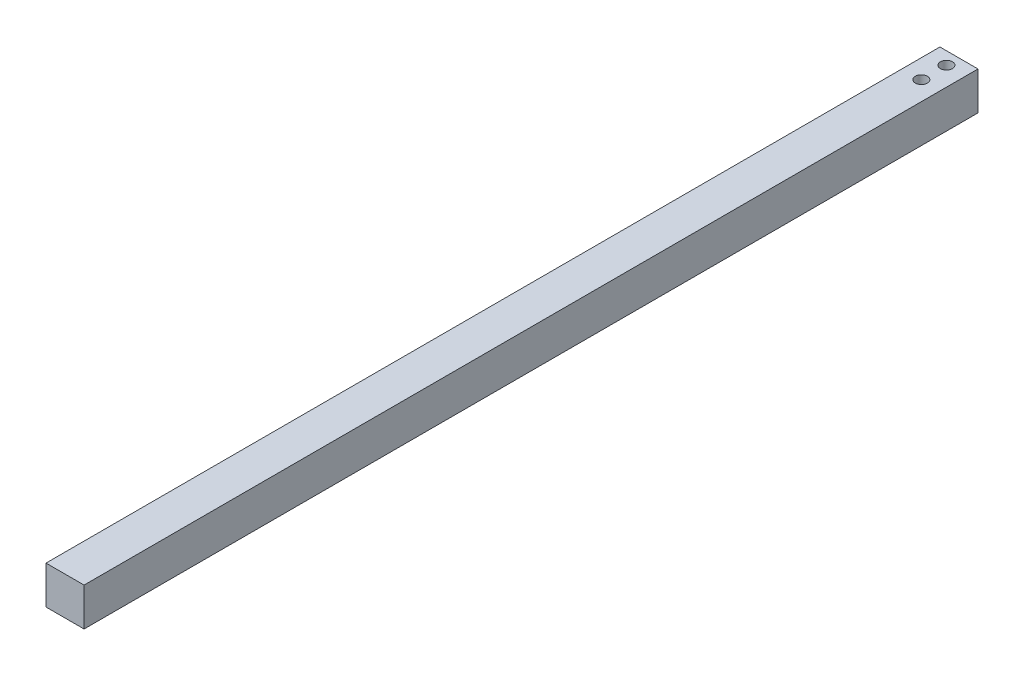
SolidWorks part; units mm, degrees
ref_plane "Front Plane" through (0, 0, 0) normal (0, 0, 1) x (1, 0, 0)
ref_plane "Top Plane" through (0, 0, 0) normal (0, 1, 0) x (1, 0, 0)
ref_plane "Right Plane" through (0, 0, 0) normal (1, 0, 0) x (0, 0, -1)
sketch "Sketch1" plane through (0, 0, 0) normal (0, 0, 1) x (1, 0, 0)
  line L1 (-9.5, -9.5) -> (9.5, -9.5)
  line L2 (-9.5, -9.5) -> (-9.5, 9.5)
  line L3 (-9.5, 9.5) -> (9.5, 9.5)
  line L4 (9.5, -9.5) -> (9.5, 9.5)
  line L5 (-9.5, -9.5) -> (9.5, 9.5) construction
  line L6 (-9.5, 9.5) -> (9.5, -9.5) construction
  point P0 (0, 0)
extrude "Boss-Extrude1" add sketch "Sketch1" along normal blind 446
sketch "Sketch2" plane through (0, -9.5, 0) normal (0, -1, 0) x (1, 0, 0)
  line L0 (-9.5, 446) -> (9.5, 446) construction
  line L1 (-9, 438.5) -> (9, 438.5)
  line L2 (-9, 438.5) -> (-9, 453.5)
  line L3 (-9, 453.5) -> (9, 453.5)
  line L4 (9, 438.5) -> (9, 453.5)
  line L5 (-9, 438.5) -> (9, 453.5) construction
  line L6 (-9, 453.5) -> (9, 438.5) construction
  line L7 (9, 446) -> (9, 438.5)
  line L8 (9, 438.5) -> (9, 442.25)
  line L9 (9, 442.25) -> (-9, 442.25)
  line L10 (9, 442.25) -> (6, 442.25)
  line L11 (0, 446) -> (0, 438.5)
  circle A0 centre (6, 442.25) radius 2
  circle A1 centre (-6, 442.25) radius 2
  point P0 (0, 446)
extrude "Cut-Extrude1" cut sketch "Sketch2" against normal blind 9 contours A1 L9 | A1 L9 | L10 A0 L9 | L9 A0 L10
sketch "Sketch3" plane through (0, 9.5, 0) normal (0, 1, 0) x (1, 0, 0)
  line L0 (9.5, 0) -> (-9.5, 0) construction
  line L1 (9.5, 0) -> (-9.5, 0)
  line L2 (0, 0) -> (0, -25)
  line L3 (0, -25) -> (0, -12.5)
  line L4 (0, -12.5) -> (-6.1481, -12.5)
  circle A0 centre (0, -18.75) radius 3
  circle A1 centre (0, -6.25) radius 3
extrude "Cut-Extrude2" cut sketch "Sketch3" against normal through all and the other way through all contours L3 A0 | A1 L2 | A1 L2 | L3 A0
